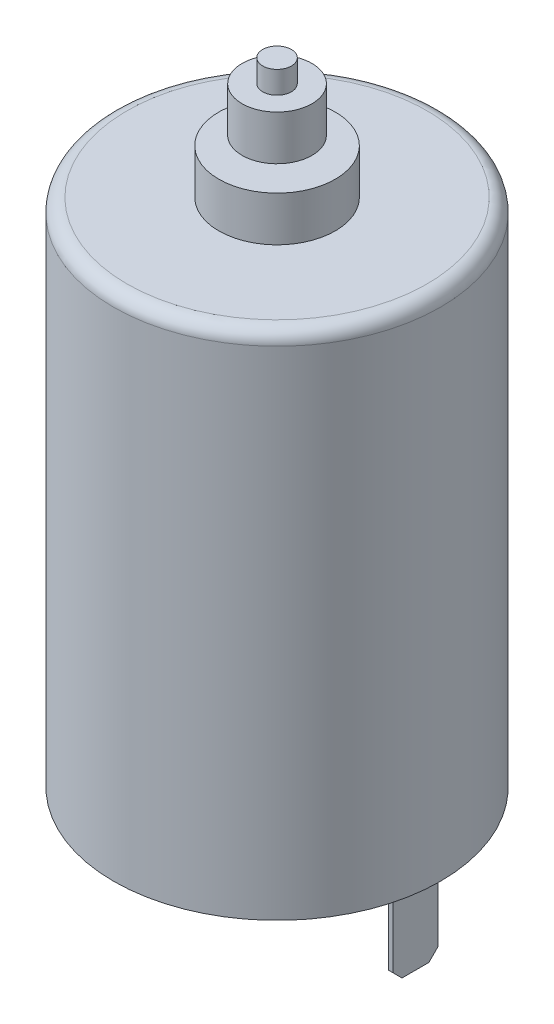
SolidWorks part; units mm, degrees
ref_plane "Front Plane" through (0, 0, 0) normal (0, 0, 1) x (1, 0, 0)
ref_plane "Top Plane" through (0, 0, 0) normal (0, 1, 0) x (1, 0, 0)
ref_plane "Right Plane" through (0, 0, 0) normal (1, 0, 0) x (0, 0, -1)
sketch "Sketch1" plane through (0, 0, 0) normal (0, 1, 0) x (1, 0, 0)
  circle A0 centre (0, 0) radius 18.25
  dimension "D1" = 36.5
extrude "Boss-Extrude1" add sketch "Sketch1" along normal blind 57
sketch "Sketch2" plane through (0, 57, 0) normal (0, 1, 0) x (1, 0, 0)
  circle A0 centre (0, 0) radius 6.5
  dimension "D1" = 13
extrude "Boss-Extrude2" add sketch "Sketch2" along normal blind 5
fillet "Fillet1" radius 1.5 1 edges at (0, 57, 18.25)
sketch "Sketch3" plane through (0, 62, 0) normal (0, 1, 0) x (1, 0, 0)
  circle A0 centre (0, 0) radius 1.6
  dimension "D1" = 3.2
extrude "Boss-Extrude3" add sketch "Sketch3" along normal blind 8.5
sketch "Sketch4" plane through (0, 70.5, 0) normal (0, 1, 0) x (1, 0, 0)
  circle A0 centre (0, 0) radius 3.9
  dimension "D1" = 7.8
extrude "Boss-Extrude4" add sketch "Sketch4" against normal blind 5 from offset 2.5 offset against normal yes
sketch "Sketch5" plane through (0, 0, 0) normal (0, -1, 0) x (1, 0, 0)
  circle A0 centre (0, 0) radius 5
  dimension "D1" = 10
extrude "Boss-Extrude5" add sketch "Sketch5" along normal blind 3
sketch "Sketch6" plane through (0, -3, 0) normal (0, -1, 0) x (1, 0, 0)
  circle A0 centre (0, 0) radius 1.5
  dimension "D1" = 3
extrude "Boss-Extrude6" add sketch "Sketch6" along normal blind 2
sketch "Sketch7" plane through (0, 0, 0) normal (0, -1, 0) x (1, 0, 0)
  line L0 (0, 0) -> (0, 12.5718) construction
  line L1 (-15.45, -2.5) -> (-14.95, 2.5) construction
  line L2 (15.45, 2.5) -> (14.95, 2.5)
  line L3 (15.45, 2.5) -> (15.45, -2.5)
  line L4 (15.45, -2.5) -> (14.95, -2.5)
  line L5 (14.95, 2.5) -> (14.95, -2.5)
  line L6 (15.45, 2.5) -> (14.95, -2.5) construction
  line L7 (15.45, -2.5) -> (14.95, 2.5) construction
  line L8 (-15.45, 2.5) -> (-14.95, -2.5) construction
  line L9 (-14.95, 2.5) -> (-14.95, -2.5)
  line L10 (-15.45, -2.5) -> (-14.95, -2.5)
  line L11 (-15.45, 2.5) -> (-15.45, -2.5)
  line L12 (-15.45, 2.5) -> (-14.95, 2.5)
  circle A1 centre (0, 0) radius 18.25 construction
  point P3 (15.2, 0)
  point P15 (-15.2, 0)
  dimension "D1" = 5
  dimension "D2" = 0.5
  dimension "D3" = 2.8
extrude "Boss-Extrude7" add sketch "Sketch7" along normal blind 10
chamfer "Chamfer1" distance 1 angle 45 4 edges at (-15.2, -10, 2.5) (-15.2, -10, -2.5) (15.2, -10, 2.5) (15.2, -10, -2.5)
